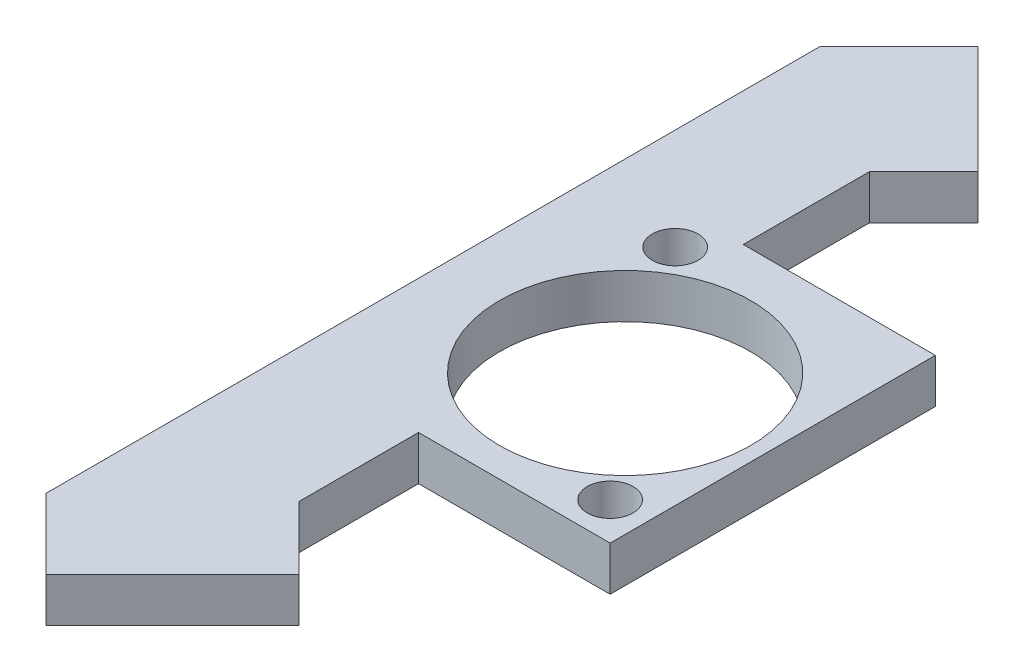
SolidWorks part; units mm, degrees
material "Custom Plastic"
ref_plane "Front Plane" through (0, 0, 0) normal (0, 0, 1) x (1, 0, 0)
ref_plane "Top Plane" through (0, 0, 0) normal (0, 1, 0) x (1, 0, 0)
ref_plane "Right Plane" through (0, 0, 0) normal (1, 0, 0) x (0, 0, -1)
sketch "Sketch1" plane through (0, 0, 0) normal (0, 1, 0) x (1, 0, 0)
  line L0 (-16.7656, 22.1767) -> (-38.7656, 0.1767) construction
  line L1 (-38.7656, 22.1767) -> (-16.7656, 22.1767)
  line L2 (-38.7656, 22.1767) -> (-38.7656, 0.1767)
  line L3 (-38.7656, 0.1767) -> (-16.7656, 0.1767)
  line L4 (-16.7656, 22.1767) -> (-16.7656, 0.1767)
  circle A1 centre (-19.3056, 2.7167) radius 1.55
  circle A2 centre (-31.9056, 19.7167) radius 1.55
  circle A3 centre (-26.2237, 10.6486) radius 8.5
  point P10 (-26.2237, 10.6486)
  dimension "D3" = 17
  dimension "D4" = 3.1
  dimension "D5" = 3.1
  dimension "D1" = 22
  dimension "D2" = 22
  dimension "D6" = 12.6
  dimension "D7" = 17
  dimension "D8" = 2.54
  dimension "D9" = 2.54
extrude "Boss-Extrude1" add sketch "Sketch1" along normal blind 3
sketch "Sketch2" plane through (0, 3, 0) normal (0, 1, 0) x (1, 0, 0)
  line L0 (-38.7656, 0.1767) -> (-38.7656, -15.9918)
  line L1 (-38.7656, 0.1767) -> (-16.7656, 0.1767) construction
  line L2 (-38.7656, -15.9918) -> (-34.0117, -20.7457)
  line L3 (-34.0117, -20.7457) -> (-25.4454, -12.1794)
  line L4 (-25.4454, -12.1794) -> (-29.7285, -7.8963)
  line L5 (-29.7285, -7.8963) -> (-29.7285, 0.1767)
  line L6 (-38.7656, 11.1767) -> (-16.7656, 11.1767) construction
  line L7 (-38.7656, 22.1767) -> (-38.7656, 0.1767) construction
  line L8 (-16.7656, 0.1767) -> (-16.7656, 22.1767) construction
  line L9 (-38.7656, 22.1767) -> (-38.7656, 36.3897)
  line L11 (-16.7656, 22.1767) -> (-38.7656, 22.1767) construction
  line L12 (-38.7656, 36.3897) -> (-33.4271, 41.7282)
  line L13 (-33.4271, 41.7282) -> (-26.0857, 34.3868)
  line L14 (-26.0857, 34.3868) -> (-29.7564, 30.7161)
  line L15 (-29.7564, 30.7161) -> (-29.7564, 22.1767)
  line L16 (-38.7656, 0.1767) -> (-29.7285, 0.1767)
  line L17 (-38.7656, 22.1767) -> (-29.7564, 22.1767)
extrude "Boss-Extrude2" add sketch "Sketch2" against normal blind 3
